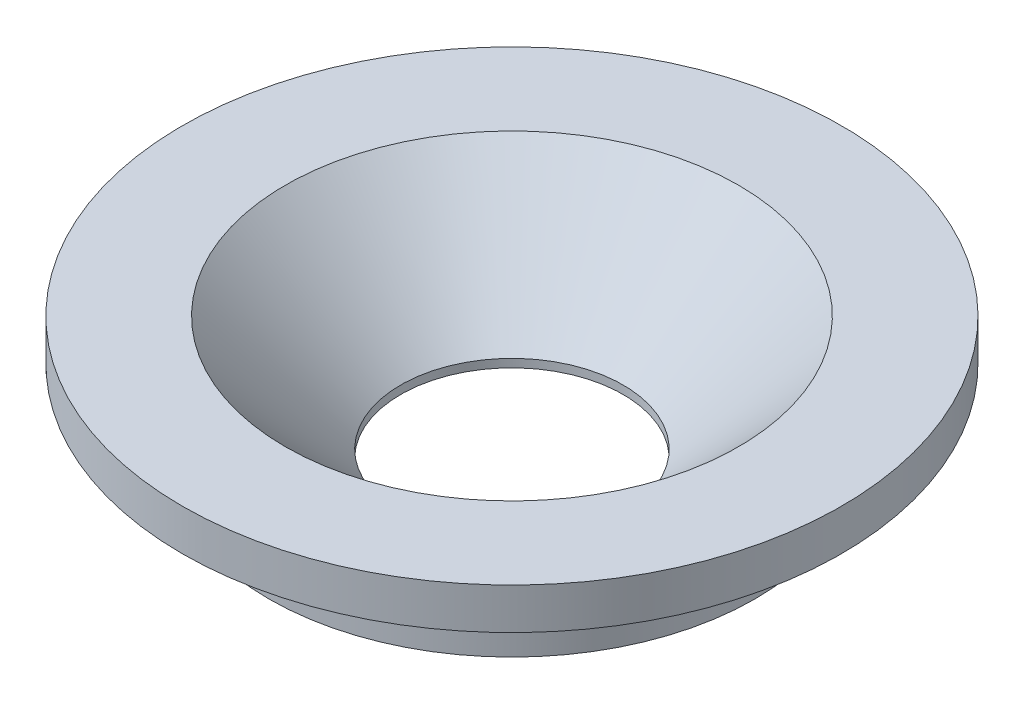
SolidWorks part; units mm, degrees
material "Plain Carbon Steel"
ref_plane "Front Plane" through (0, 0, 0) normal (0, 0, 1) x (1, 0, 0)
ref_plane "Top Plane" through (0, 0, 0) normal (0, 1, 0) x (1, 0, 0)
ref_plane "Right Plane" through (0, 0, 0) normal (1, 0, 0) x (0, 0, -1)
sketch "Sketch1" plane through (0, 0, 0) normal (0, 1, 0) x (1, 0, 0)
  circle A0 centre (0, 0) radius 2.95
extrude "Boss-Extrude1" add sketch "Sketch1" along normal blind 1
sketch "Sketch2" plane through (0, 1, 0) normal (0, 1, 0) x (1, 0, 0)
  circle A0 centre (0, 0) radius 4
extrude "Boss-Extrude2" add sketch "Sketch2" along normal blind 0.5
hole_wizard "CSK for M2.5 Flat Head Machine Screw1" positions "3DSketch1" profile "Sketch3" countersink size "M2.5" standard "ANSI Metric"
sketch3d "3DSketch1"
  line L0 (0, 1.5, 0) -> (0, 1, 0) construction
  point P0 (0, 1.5, 0)
sketch "Sketch3" plane through (0, 1.5, 0) normal (1, 0, 0) x (0, 0, 1)
  line L0 (0, 0) -> (0, 2.3112)
  line L1 (0, 2.3112) -> (1.35, 1.5)
  line L2 (1.35, 1.5) -> (1.35, 1.4)
  line L3 (1.35, 1.4) -> (2.75, 0)
  line L5 (2.75, 0) -> (0, 0)
  line L6 (-1.35, 1.4) -> (-2.75, 0) construction
  line L10 (0, 2.3112) -> (-1.35, 1.5) construction
  line L11 (0, -6.35) -> (0, 107.95) construction
  dimension "Hole Dia." = 2.7
  dimension "Hole Depth" = 1.5
  dimension "Near C'Sink Dia." = 5.5
  dimension "Near C'Sink Angle" = 90
  dimension "Drill Angle" = 118
